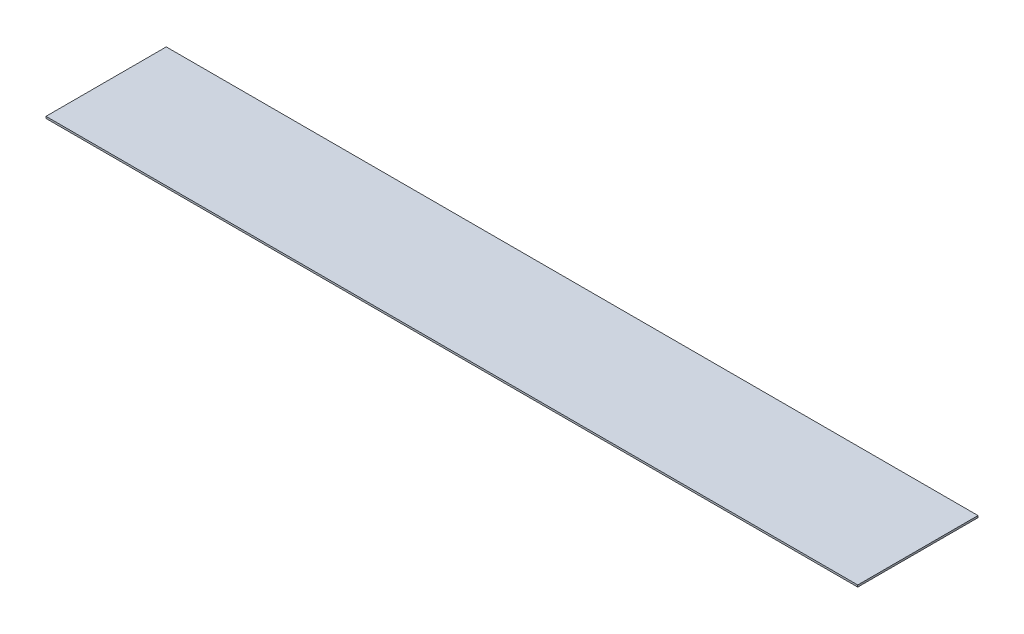
SolidWorks part; units mm, degrees
material "Nylon 101"
ref_plane "Front Plane" through (0, 0, 0) normal (0, 0, 1) x (1, 0, 0)
ref_plane "Top Plane" through (0, 0, 0) normal (0, 1, 0) x (1, 0, 0)
ref_plane "Right Plane" through (0, 0, 0) normal (1, 0, 0) x (0, 0, -1)
sketch "Sketch1" plane through (0, 0, 0) normal (0, 1, 0) x (1, 0, 0)
  line L1 (0, 0) -> (685.8, 0)
  line L2 (0, 0) -> (0, 101.6)
  line L3 (0, 101.6) -> (685.8, 101.6)
  line L4 (685.8, 0) -> (685.8, 101.6)
  dimension "D1" = 101.6
  dimension "D2" = 685.8
extrude "Boss-Extrude1" add sketch "Sketch1" along normal blind 1.5875
